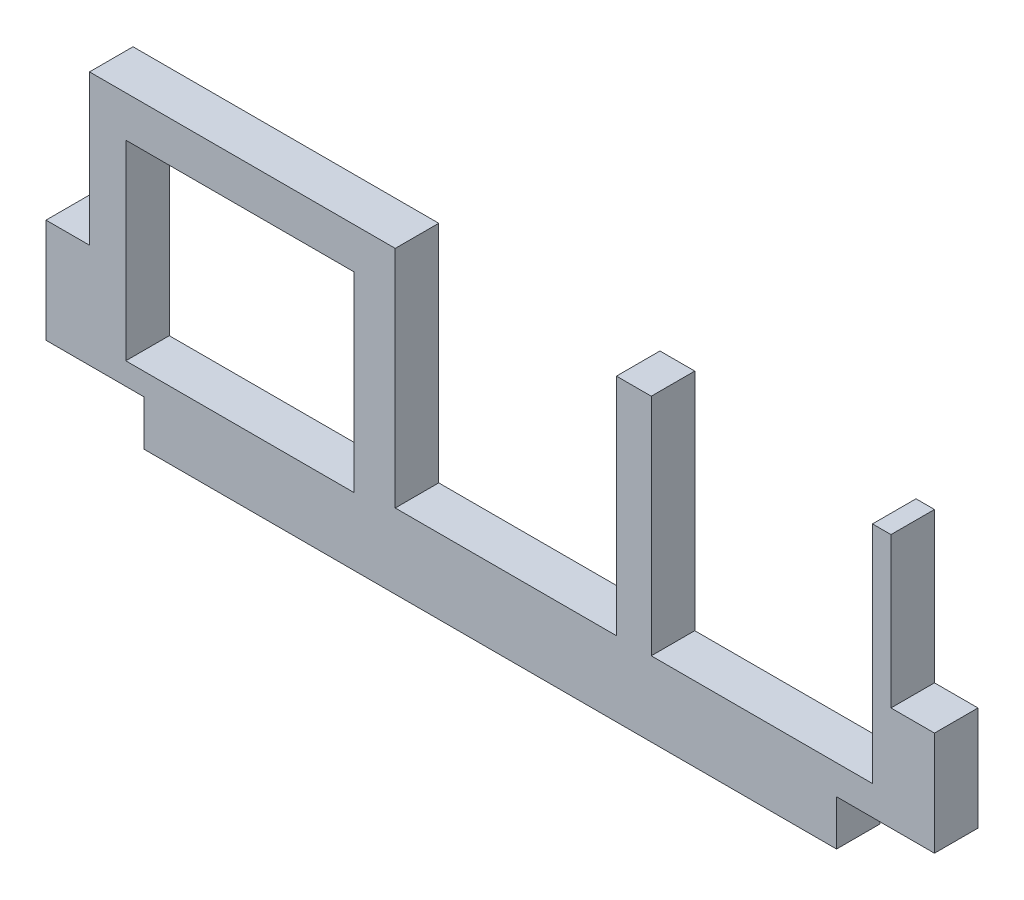
SolidWorks part; units mm, degrees
ref_plane "Front Plane" through (0, 0, 0) normal (0, 0, 1) x (1, 0, 0)
ref_plane "Top Plane" through (0, 0, 0) normal (0, 1, 0) x (1, 0, 0)
ref_plane "Right Plane" through (0, 0, 0) normal (1, 0, 0) x (0, 0, -1)
sketch "Sketch1" plane through (0, 0, 0) normal (0, 0, 1) x (1, 0, 0)
  line L7 (-3.048, 12.0142) -> (0, 12.0142)
  line L8 (-3.048, 12.0142) -> (-3.048, 4.7244)
  line L9 (3.81, 1.5494) -> (3.81, 4.7244)
  line L10 (3.81, 1.5494) -> (52.324, 1.5494)
  line L11 (52.324, 1.5494) -> (52.324, 4.7244)
  line L12 (59.182, 12.0142) -> (56.134, 12.0142)
  line L13 (59.182, 4.7244) -> (59.182, 12.0142)
  line L14 (-3.048, 4.7244) -> (3.81, 4.7244)
  line L15 (52.324, 4.7244) -> (59.182, 4.7244)
  line L16 (0, 12.0142) -> (0, 19.6596)
  line L17 (0, 27.2034) -> (0, 4.7244) construction
  line L18 (0, 19.6596) -> (2.54, 19.6596)
  line L19 (2.54, 19.6596) -> (2.54, 6.2738)
  line L20 (2.54, 6.2738) -> (18.542, 6.2738)
  line L21 (18.542, 6.2738) -> (18.542, 22.5298)
  line L22 (18.542, 22.5298) -> (21.4122, 22.5298)
  line L23 (21.4122, 22.5298) -> (21.4122, 6.7818)
  line L24 (21.4122, 6.7818) -> (36.9062, 6.7818)
  line L25 (36.9062, 6.7818) -> (36.9062, 22.5298)
  line L26 (36.9062, 22.5298) -> (39.3446, 22.5298)
  line L27 (39.3446, 22.5298) -> (39.3446, 6.7818)
  line L28 (39.3446, 6.7818) -> (54.8386, 6.7818)
  line L29 (54.8386, 6.7818) -> (54.8386, 22.5298)
  line L30 (54.8386, 22.5298) -> (56.134, 22.5298)
  line L31 (56.134, 27.2034) -> (56.134, 4.7244) construction
  line L32 (56.134, 22.5298) -> (56.134, 12.0142)
  dimension "D1" = 14.9352
  dimension "D2" = 2.54
  dimension "D3" = 2.8702
  dimension "D4" = 2.4384
  dimension "D5" = 15.494
  dimension "D6" = 16.002
  dimension "D7" = 1.5494
  dimension "D8" = 15.748
  dimension "D9" = 2.0574
extrude "Boss-Extrude1" add sketch "Sketch1" along normal blind 3.048
sketch "Sketch2" plane through (0, 0, 3.048) normal (0, 0, 1) x (1, 0, 0)
  line L1 (0, 19.6596) -> (18.542, 19.6596)
  line L2 (0, 19.6596) -> (0, 22.5298)
  line L3 (0, 22.5298) -> (18.542, 22.5298)
  line L4 (18.542, 19.6596) -> (18.542, 22.5298)
extrude "Boss-Extrude2" add sketch "Sketch2" against normal up to vertex (3.048 mm away) up to point (18.542, 22.5298, 0)
